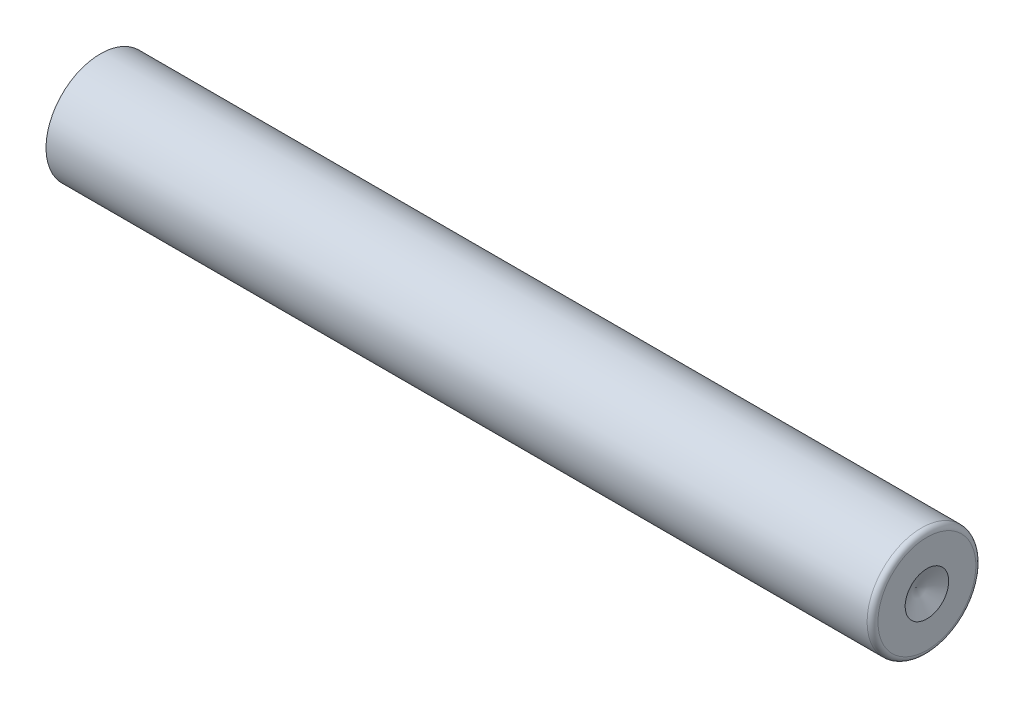
SolidWorks part; units mm, degrees
material "AISI 316 Barra de acero inoxidable recocido (SS)"
ref_plane "Alzado" through (0, 0, 0) normal (0, 0, 1) x (1, 0, 0)
ref_plane "Planta" through (0, 0, 0) normal (0, 1, 0) x (1, 0, 0)
ref_plane "Vista lateral" through (0, 0, 0) normal (1, 0, 0) x (0, 0, -1)
sketch "Croquis1" plane through (0, 0, 0) normal (0, 0, 1) x (1, 0, 0)
  line L1 (0, 0) -> (38, 0)
  line L2 (0, 0) -> (0, 2.5)
  line L3 (0, 2.5) -> (38, 2.5)
  line L4 (38, 0) -> (38, 2.5)
  dimension "D1" = 2.5
  dimension "D2" = 38
revolve "Revolución1" add sketch "Croquis1" angle 360 about L1
fillet "Redondeo1" radius 0.25 1 edges at (38, 0, 2.5)
sketch "Croquis3" plane through (0, 0, 0) normal (0, 0, 1) x (1, 0, 0)
  line L0 (38, 0) -> (37.5, 0)
  line L1 (38, -2.25) -> (38, 2.25) construction
  line L2 (37.5, 0) -> (38, 1)
  line L3 (38, 1) -> (38, 0)
  dimension "D1" = 0.5
  dimension "D2" = 1
revolve "Cortar-Revolución1" cut sketch "Croquis3" angle 360 about L0
